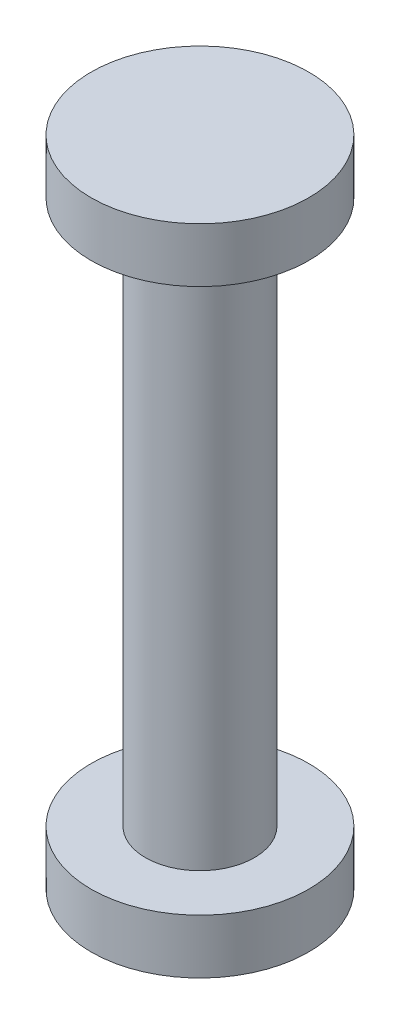
SolidWorks part; units mm, degrees
ref_plane "Front Plane" through (0, 0, 0) normal (0, 0, 1) x (1, 0, 0)
ref_plane "Top Plane" through (0, 0, 0) normal (0, 1, 0) x (1, 0, 0)
ref_plane "Right Plane" through (0, 0, 0) normal (1, 0, 0) x (0, 0, -1)
sketch "Sketch1" plane through (0, 0, 0) normal (0, 1, 0) x (1, 0, 0)
  circle A0 centre (0, 0) radius 5
  dimension "D1" = 10
extrude "Boss-Extrude1" add sketch "Sketch1" along normal blind 50
sketch "Sketch2" plane through (0, 50, 0) normal (0, 1, 0) x (1, 0, 0)
  circle A0 centre (0, 0) radius 10
  dimension "D1" = 20
extrude "Boss-Extrude2" add sketch "Sketch2" along normal blind 5
ref_plane "Plane1" through (0, 25, 0) normal (0, -1, 0) x (-1, 0, 0)
mirror "Mirror1" about plane through (0, 25, 0) normal (0, -1, 0) of "Boss-Extrude2"
